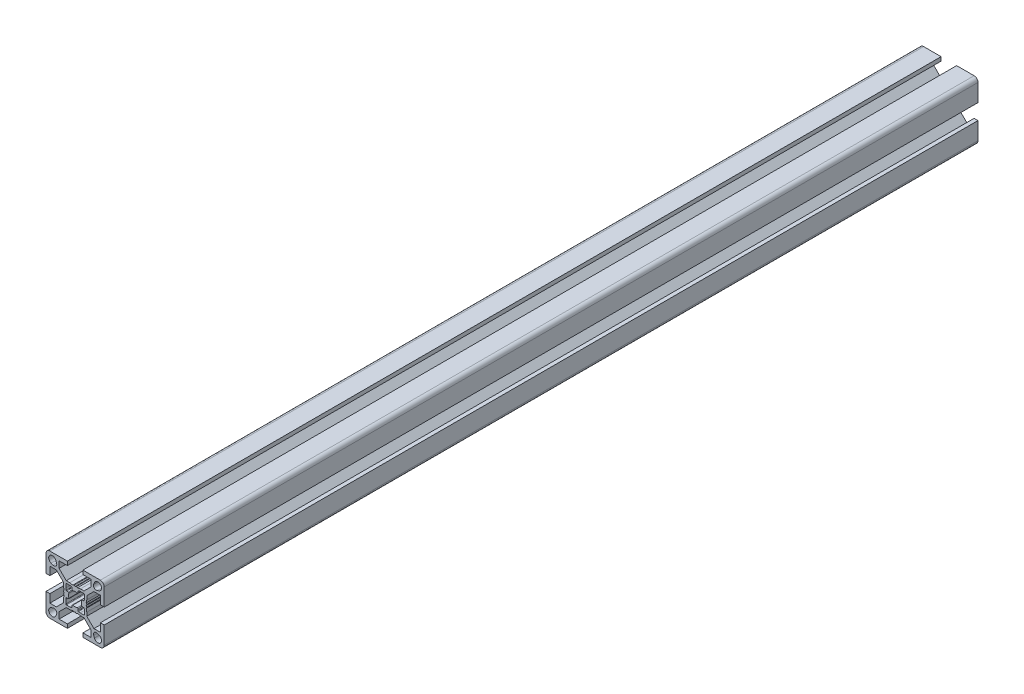
SolidWorks part; units mm, degrees
material "6063-T5"
ref_plane "Piano frontale" through (0, 0, 0) normal (0, 0, 1) x (1, 0, 0)
ref_plane "Piano superiore" through (0, 0, 0) normal (0, 1, 0) x (1, 0, 0)
ref_plane "Piano destro" through (0, 0, 0) normal (1, 0, 0) x (0, 0, -1)
ref_plane "Piano1" through (0, 0, -450) normal (0, 0, -1) x (-1, 0, 0)
sketch "Schizzo1" plane through (0, 0, -450) normal (0, 0, -1) x (-1, 0, 0)
  line L0 (9.9189, -12.3615) -> (9.5391, -11.3389)
  line L1 (11.3389, -9.5391) -> (12.3615, -9.9189)
  line L2 (12.3615, 9.9189) -> (11.3389, 9.5391)
  line L3 (9.5391, 11.3389) -> (9.9189, 12.3615)
  line L4 (-9.5391, -11.3389) -> (-9.9189, -12.3615)
  line L5 (-12.3615, -9.9189) -> (-11.3389, -9.5391)
  line L6 (-11.3389, 9.5391) -> (-12.3615, 9.9189)
  line L7 (-9.9189, 12.3615) -> (-9.5391, 11.3389)
  line L8 (4.8, -2.6444) -> (4.8, -4.5)
  line L9 (4.5, -4.8) -> (2.6444, -4.8)
  line L10 (2.5872, -4.7945) -> (1.7428, -4.6303)
  line L11 (1.5, -4.3359) -> (1.5, -3.5)
  line L12 (-1.5, -3.5) -> (-1.5, -4.3359)
  line L13 (-1.7428, -4.6303) -> (-2.5872, -4.7945)
  line L14 (-2.6444, -4.8) -> (-4.5, -4.8)
  line L15 (-4.8, -4.5) -> (-4.8, -2.6444)
  line L16 (-4.7945, -2.5872) -> (-4.6303, -1.7428)
  line L17 (-4.3359, -1.5) -> (-3.5, -1.5)
  line L18 (-3.5, 1.5) -> (-4.3359, 1.5)
  line L19 (-4.6303, 1.7428) -> (-4.7945, 2.5872)
  line L20 (-4.8, 2.6444) -> (-4.8, 4.5)
  line L21 (-4.5, 4.8) -> (-2.6444, 4.8)
  line L22 (-2.5872, 4.7945) -> (-1.7428, 4.6303)
  line L23 (-1.5, 4.3359) -> (-1.5, 3.5)
  line L24 (1.5, 3.5) -> (1.5, 4.3359)
  line L25 (1.7428, 4.6303) -> (2.5872, 4.7945)
  line L26 (2.6444, 4.8) -> (4.5, 4.8)
  line L27 (4.8, 4.5) -> (4.8, 2.6444)
  line L28 (4.7945, 2.5872) -> (4.6303, 1.7428)
  line L29 (4.3359, 1.5) -> (3.5, 1.5)
  line L30 (3.5, -1.5) -> (4.3359, -1.5)
  line L31 (4.6303, -1.7428) -> (4.7945, -2.5872)
  line L32 (9.6642, 8.25) -> (13, 8.25)
  line L33 (13, 8.25) -> (13, 4)
  line L34 (13, 4) -> (15, 4)
  line L35 (15, 4) -> (15, 13)
  line L36 (13, 15) -> (4, 15)
  line L37 (4, 15) -> (4, 13)
  line L38 (4, 13) -> (8.25, 13)
  line L39 (8.25, 13) -> (8.25, 9.6642)
  line L40 (4.5858, 6) -> (2.7434, 6)
  line L41 (2.7434, 6) -> (1.2, 5.7)
  line L42 (1.2, 5.7) -> (0.75, 5.9598)
  line L43 (0.45, 5.9598) -> (0, 5.7)
  line L44 (0, 5.7) -> (-0.45, 5.9598)
  line L45 (-0.75, 5.9598) -> (-1.2, 5.7)
  line L46 (-1.2, 5.7) -> (-2.7434, 6)
  line L47 (-2.7434, 6) -> (-4.5858, 6)
  line L48 (-8.25, 9.6642) -> (-8.25, 13)
  line L49 (-8.25, 13) -> (-4, 13)
  line L50 (-4, 13) -> (-4, 15)
  line L51 (-4, 15) -> (-13, 15)
  line L52 (-15, 13) -> (-15, 4)
  line L53 (-15, 4) -> (-13, 4)
  line L54 (-13, 4) -> (-13, 8.25)
  line L55 (-13, 8.25) -> (-9.6642, 8.25)
  line L56 (-6, 4.5858) -> (-6, 2.7434)
  line L57 (-6, 2.7434) -> (-5.7, 1.2)
  line L58 (-5.7, 1.2) -> (-5.9598, 0.75)
  line L59 (-5.9598, 0.45) -> (-5.7, 0)
  line L60 (-5.7, 0) -> (-5.9598, -0.45)
  line L61 (-5.9598, -0.75) -> (-5.7, -1.2)
  line L62 (-5.7, -1.2) -> (-6, -2.7434)
  line L63 (-6, -2.7434) -> (-6, -4.5858)
  line L64 (-9.6642, -8.25) -> (-13, -8.25)
  line L65 (-13, -8.25) -> (-13, -4)
  line L66 (-13, -4) -> (-15, -4)
  line L67 (-15, -4) -> (-15, -13)
  line L68 (-13, -15) -> (-4, -15)
  line L69 (-4, -15) -> (-4, -13)
  line L70 (-4, -13) -> (-8.25, -13)
  line L71 (-8.25, -13) -> (-8.25, -9.6642)
  line L72 (-4.5858, -6) -> (-2.7434, -6)
  line L73 (-2.7434, -6) -> (-1.2, -5.7)
  line L74 (-1.2, -5.7) -> (-0.75, -5.9598)
  line L75 (-0.45, -5.9598) -> (0, -5.7)
  line L76 (0, -5.7) -> (0.45, -5.9598)
  line L77 (0.75, -5.9598) -> (1.2, -5.7)
  line L78 (1.2, -5.7) -> (2.7434, -6)
  line L79 (2.7434, -6) -> (4.5858, -6)
  line L80 (8.25, -9.6642) -> (8.25, -13)
  line L81 (8.25, -13) -> (4, -13)
  line L82 (4, -13) -> (4, -15)
  line L83 (4, -15) -> (13, -15)
  line L84 (15, -13) -> (15, -4)
  line L85 (15, -4) -> (13, -4)
  line L86 (13, -4) -> (13, -8.25)
  line L87 (13, -8.25) -> (9.6642, -8.25)
  line L88 (6, -4.5858) -> (6, -2.7434)
  line L89 (6, -2.7434) -> (5.7, -1.2)
  line L90 (5.7, -1.2) -> (5.9598, -0.75)
  line L91 (5.9598, -0.45) -> (5.7, 0)
  line L92 (5.7, 0) -> (5.9598, 0.45)
  line L93 (5.9598, 0.75) -> (5.7, 1.2)
  line L94 (5.7, 1.2) -> (6, 2.7434)
  line L95 (6, 2.7434) -> (6, 4.5858)
  arc A0 (12.3615, -9.9189) -> (9.9189, -12.3615) centre (11.7, -11.7) cw
  arc A1 (9.5391, -11.3389) -> (11.3389, -9.5391) centre (10.8515, -10.8515) cw
  arc A2 (9.9189, 12.3615) -> (12.3615, 9.9189) centre (11.7, 11.7) cw
  arc A3 (11.3389, 9.5391) -> (9.5391, 11.3389) centre (10.8515, 10.8515) cw
  arc A4 (-9.9189, -12.3615) -> (-12.3615, -9.9189) centre (-11.7, -11.7) cw
  arc A5 (-11.3389, -9.5391) -> (-9.5391, -11.3389) centre (-10.8515, -10.8515) cw
  arc A6 (-12.3615, 9.9189) -> (-9.9189, 12.3615) centre (-11.7, 11.7) cw
  arc A7 (-9.5391, 11.3389) -> (-11.3389, 9.5391) centre (-10.8515, 10.8515) cw
  arc A8 (4.8, -4.5) -> (4.5, -4.8) centre (4.5, -4.5) cw
  arc A9 (2.6444, -4.8) -> (2.5872, -4.7945) centre (2.6444, -4.5) cw
  arc A10 (1.7428, -4.6303) -> (1.5, -4.3359) centre (1.8, -4.3359) cw
  arc A11 (1.5, -3.5) -> (1.1027, -3.2162) centre (1.2, -3.5) ccw
  arc A12 (1.1027, -3.2162) -> (-1.1027, -3.2162) centre (0, 0) cw
  arc A13 (-1.1027, -3.2162) -> (-1.5, -3.5) centre (-1.2, -3.5) ccw
  arc A14 (-1.5, -4.3359) -> (-1.7428, -4.6303) centre (-1.8, -4.3359) cw
  arc A15 (-2.5872, -4.7945) -> (-2.6444, -4.8) centre (-2.6444, -4.5) cw
  arc A16 (-4.5, -4.8) -> (-4.8, -4.5) centre (-4.5, -4.5) cw
  arc A17 (-4.8, -2.6444) -> (-4.7945, -2.5872) centre (-4.5, -2.6444) cw
  arc A18 (-4.6303, -1.7428) -> (-4.3359, -1.5) centre (-4.3359, -1.8) cw
  arc A19 (-3.5, -1.5) -> (-3.2162, -1.1027) centre (-3.5, -1.2) ccw
  arc A20 (-3.2162, -1.1027) -> (-3.2162, 1.1027) centre (0, 0) cw
  arc A21 (-3.2162, 1.1027) -> (-3.5, 1.5) centre (-3.5, 1.2) ccw
  arc A22 (-4.3359, 1.5) -> (-4.6303, 1.7428) centre (-4.3359, 1.8) cw
  arc A23 (-4.7945, 2.5872) -> (-4.8, 2.6444) centre (-4.5, 2.6444) cw
  arc A24 (-4.8, 4.5) -> (-4.5, 4.8) centre (-4.5, 4.5) cw
  arc A25 (-2.6444, 4.8) -> (-2.5872, 4.7945) centre (-2.6444, 4.5) cw
  arc A26 (-1.7428, 4.6303) -> (-1.5, 4.3359) centre (-1.8, 4.3359) cw
  arc A27 (-1.5, 3.5) -> (-1.1027, 3.2162) centre (-1.2, 3.5) ccw
  arc A28 (-1.1027, 3.2162) -> (1.1027, 3.2162) centre (0, 0) cw
  arc A29 (1.1027, 3.2162) -> (1.5, 3.5) centre (1.2, 3.5) ccw
  arc A30 (1.5, 4.3359) -> (1.7428, 4.6303) centre (1.8, 4.3359) cw
  arc A31 (2.5872, 4.7945) -> (2.6444, 4.8) centre (2.6444, 4.5) cw
  arc A32 (4.5, 4.8) -> (4.8, 4.5) centre (4.5, 4.5) cw
  arc A33 (4.8, 2.6444) -> (4.7945, 2.5872) centre (4.5, 2.6444) cw
  arc A34 (4.6303, 1.7428) -> (4.3359, 1.5) centre (4.3359, 1.8) cw
  arc A35 (3.5, 1.5) -> (3.2162, 1.1027) centre (3.5, 1.2) ccw
  arc A36 (3.2162, 1.1027) -> (3.2162, -1.1027) centre (0, 0) cw
  arc A37 (3.2162, -1.1027) -> (3.5, -1.5) centre (3.5, -1.2) ccw
  arc A38 (4.3359, -1.5) -> (4.6303, -1.7428) centre (4.3359, -1.8) cw
  arc A39 (4.7945, -2.5872) -> (4.8, -2.6444) centre (4.5, -2.6444) cw
  arc A40 (15, 13) -> (13, 15) centre (13, 13) ccw
  arc A41 (0.75, 5.9598) -> (0.45, 5.9598) centre (0.6, 5.7) ccw
  arc A42 (-0.45, 5.9598) -> (-0.75, 5.9598) centre (-0.6, 5.7) ccw
  arc A43 (-13, 15) -> (-15, 13) centre (-13, 13) ccw
  arc A44 (-5.9598, 0.75) -> (-5.9598, 0.45) centre (-5.7, 0.6) ccw
  arc A45 (-5.9598, -0.45) -> (-5.9598, -0.75) centre (-5.7, -0.6) ccw
  arc A46 (-15, -13) -> (-13, -15) centre (-13, -13) ccw
  arc A47 (-0.75, -5.9598) -> (-0.45, -5.9598) centre (-0.6, -5.7) ccw
  arc A48 (0.45, -5.9598) -> (0.75, -5.9598) centre (0.6, -5.7) ccw
  arc A49 (13, -15) -> (15, -13) centre (13, -13) ccw
  arc A50 (5.9598, -0.75) -> (5.9598, -0.45) centre (5.7, -0.6) ccw
  arc A51 (5.9598, 0.45) -> (5.9598, 0.75) centre (5.7, 0.6) ccw
  spline S0 degree 3 poles (6, 4.5858) (7.2214, 5.8072) (8.4428, 7.0286) (9.6642, 8.25) knots 0 0 0 0 1 1 1 1
  spline S1 degree 3 poles (8.25, 9.6642) (7.0286, 8.4428) (5.8072, 7.2214) (4.5858, 6) knots 0 0 0 0 1 1 1 1
  spline S2 degree 3 poles (-4.5858, 6) (-5.8072, 7.2214) (-7.0286, 8.4428) (-8.25, 9.6642) knots 0 0 0 0 1 1 1 1
  spline S3 degree 3 poles (-9.6642, 8.25) (-8.4428, 7.0286) (-7.2214, 5.8072) (-6, 4.5858) knots 0 0 0 0 1 1 1 1
  spline S4 degree 3 poles (-6, -4.5858) (-7.2214, -5.8072) (-8.4428, -7.0286) (-9.6642, -8.25) knots 0 0 0 0 1 1 1 1
  spline S5 degree 3 poles (-8.25, -9.6642) (-7.0286, -8.4428) (-5.8072, -7.2214) (-4.5858, -6) knots 0 0 0 0 1 1 1 1
  spline S6 degree 3 poles (4.5858, -6) (5.8072, -7.2214) (7.0286, -8.4428) (8.25, -9.6642) knots 0 0 0 0 1 1 1 1
  spline S7 degree 3 poles (9.6642, -8.25) (8.4428, -7.0286) (7.2214, -5.8072) (6, -4.5858) knots 0 0 0 0 1 1 1 1
extrude "Estrusione-Estrusione1" add sketch "Schizzo1" against normal blind 450
